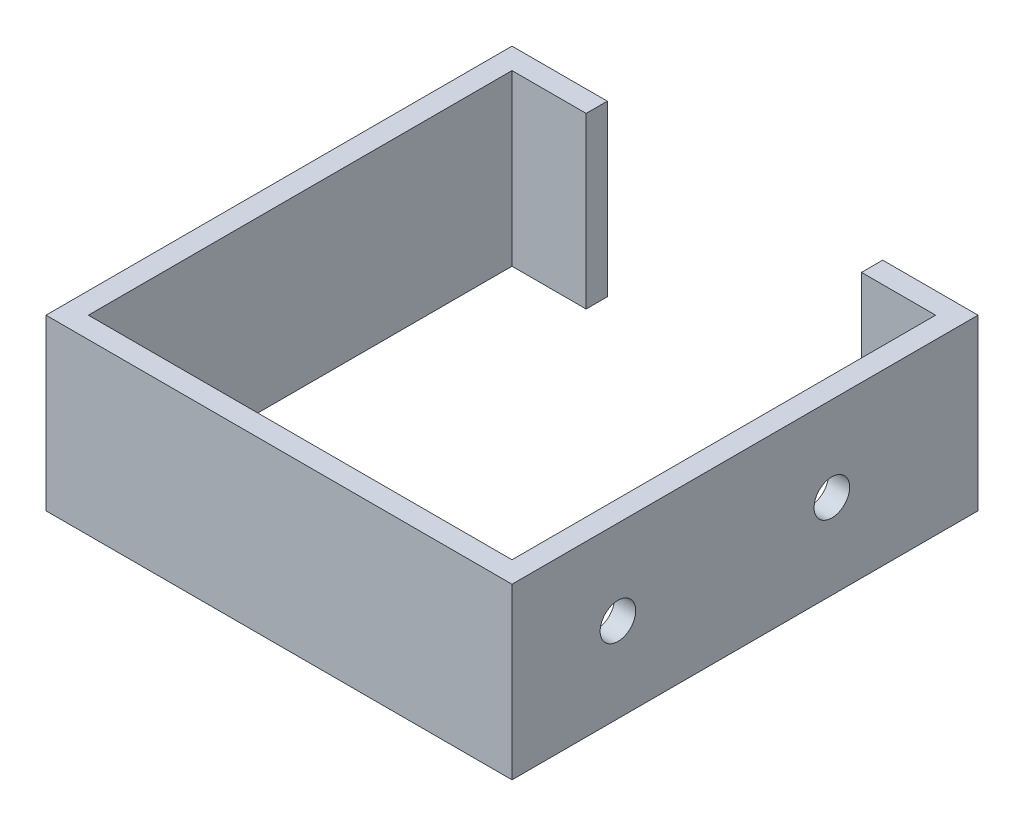
SolidWorks part; units mm, degrees
ref_plane "Front" through (0, 0, 0) normal (0, 0, 1) x (1, 0, 0)
ref_plane "Top" through (0, 0, 0) normal (0, 1, 0) x (1, 0, 0)
ref_plane "Right" through (0, 0, 0) normal (1, 0, 0) x (0, 0, -1)
sketch "Sketch1" plane through (0, 0, 0) normal (0, 1, 0) x (1, 0, 0)
  line L0 (-3.175, -3.175) -> (-3.175, 63.5)
  line L1 (0, 0) -> (63.5, 0)
  line L2 (0, 0) -> (0, 63.5)
  line L4 (63.5, 0) -> (63.5, 63.5)
  line L5 (-3.175, -3.175) -> (66.675, -3.175)
  line L6 (66.675, -3.175) -> (66.675, 63.5)
  line L10 (0, 63.5) -> (11.1125, 63.5)
  line L11 (-3.175, 63.5) -> (-3.175, 66.675)
  line L12 (-3.175, 66.675) -> (11.1125, 66.675)
  line L13 (11.1125, 63.5) -> (11.1125, 66.675)
  line L14 (63.5, 63.5) -> (52.3875, 63.5)
  line L15 (66.675, 63.5) -> (66.675, 66.675)
  line L16 (66.675, 66.675) -> (52.3875, 66.675)
  line L17 (52.3875, 63.5) -> (52.3875, 66.675)
  dimension "D1" = 63.5
  dimension "D2" = 63.5
  dimension "D4" = 3.175
  dimension "D5" = 14.2875
  dimension "D3" = 3.175
extrude "Boss-Extrude1" add sketch "Sketch1" along normal blind 25.4
sketch "Sketch2" plane through (66.675, 0, 0) normal (1, 0, 0) x (0, 0, -1)
  circle A0 centre (12.7, 12.7) radius 2.667 construction
  circle A1 centre (12.7, 12.7) radius 2.667
  circle A2 centre (44.7675, 12.7) radius 2.667 construction
  circle A3 centre (44.7675, 12.7) radius 2.667
extrude "Cut-Extrude1" cut sketch "Sketch2" against normal up to next
